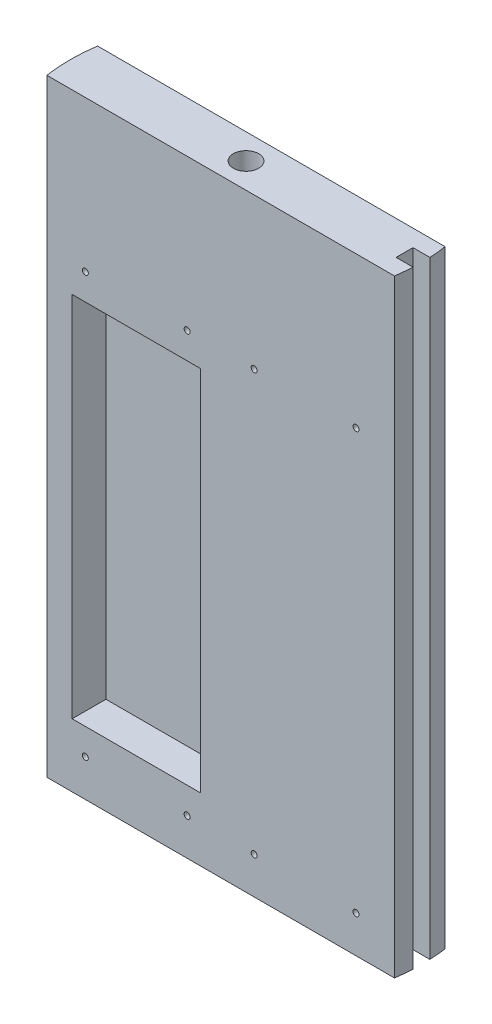
SolidWorks part; units mm, degrees
material "PE High Density"
ref_plane "Front" through (0, 0, 0) normal (0, 0, 1) x (1, 0, 0)
ref_plane "Top" through (0, 0, 0) normal (0, 1, 0) x (1, 0, 0)
ref_plane "Right" through (0, 0, 0) normal (1, 0, 0) x (0, 0, -1)
sketch "Sketch1" plane through (0, 0, 0) normal (0, 1, 0) x (1, 0, 0)
  line L0 (0, 9.525) -> (0, -9.525) construction
  line L1 (-65.3495, -9.525) -> (65.3495, -9.525)
  line L3 (-65.3495, 9.525) -> (65.3495, 9.525)
  arc A0 (-65.3495, 9.525) -> (-65.3495, -9.525) centre (0, 0) ccw
  circle A1 centre (0, 0) radius 66.04 construction
  arc A2 (65.3495, -9.525) -> (65.3495, 9.525) centre (0, 0) ccw
  point P0 (0, 0)
  point P3 (0, 0)
  dimension "D1" = 19.05
extrude "Boss-Extrude1" add sketch "Sketch1" against normal up to surface (228.6 mm away)
sketch "Sketch3" plane through (0, 0, 0) normal (0, 1, 0) x (1, 0, 0)
  line L0 (66.04, 0) -> (33.02, 0) construction
  line L1 (33.02, 0) -> (0, 0) construction
  line L2 (0, 0) -> (-33.02, 0) construction
  line L3 (-33.02, 0) -> (-66.04, 0) construction
  circle A0 centre (0, 0) radius 4.7625
  arc A3 (65.3495, -9.525) -> (65.3495, 9.525) centre (0, 0) ccw construction
  arc A4 (-65.3495, 9.525) -> (-65.3495, -9.525) centre (0, 0) ccw construction
  dimension "D1" = 9.525
extrude "Cut-Extrude1" cut sketch "Sketch3" against normal through all contours A0
hole_wizard "#4-40 Tapped Hole1" positions "Sketch4" profile "Sketch5" tap size "#4-40" standard "ANSI Inch" end condition through all
sketch "Sketch4" plane through (0, 0, 9.525) normal (0, 0, 1) x (1, 0, 0)
  point P0 (-50.8954, -56.7192)
  point P3 (-12.6046, -56.7192)
  point P15 (-12.6046, -214.6808)
  point P24 (-50.8954, -214.6808)
  point P32 (12.6046, -56.7192)
  point P35 (50.8954, -56.7192)
  point P40 (12.6046, -214.6808)
  point P43 (50.8954, -214.6808)
cosmetic thread "Hole Thread1" parameters "D2"=2.8448
cosmetic thread "Hole Thread8" parameters "D2"=2.8448
cosmetic thread "Hole Thread13" parameters "D2"=2.8448
cosmetic thread "Hole Thread14" parameters "D2"=2.8448
sketch "Sketch5" plane through (-50.8954, -56.7192, 9.525) normal (1, 0, 0) x (0, -1, 0)
  line L0 (0, 0) -> (0, 19.05)
  line L1 (0, 19.05) -> (1.1303, 19.05)
  line L2 (1.1303, 19.05) -> (1.1303, 0)
  line L5 (1.1303, 0) -> (0, 0)
  line L11 (0, -6.35) -> (0, 107.95) construction
  dimension "Thru Tap Drill Dia." = 2.2606
  dimension "Thru Tap Drill Depth" = 19.05
cosmetic thread "Hole Thread17" parameters "D2"=2.8448
cosmetic thread "Hole Thread18" parameters "D2"=2.8448
cosmetic thread "Hole Thread19" parameters "D2"=2.8448
cosmetic thread "Hole Thread20" parameters "D2"=2.8448
sketch "Sketch6" plane through (0, -228.6, 0) normal (0, -1, 0) x (1, 0, 0)
  line L0 (59.6136, -3.175) -> (65.9636, -3.175) construction
  line L1 (59.6136, 3.175) -> (65.9636, 3.175)
  line L2 (59.6136, 3.175) -> (59.6136, -3.175)
  line L3 (59.6136, -3.175) -> (65.9636, -3.175)
  arc A0 (65.3495, -9.525) -> (65.3495, 9.525) centre (0, 0) ccw construction
  arc A1 (65.9636, 3.175) -> (65.9636, -3.175) centre (0, 0) cw
extrude "Cut-Extrude2" cut sketch "Sketch6" against normal through all
sketch "Sketch7" plane through (0, 0, 9.525) normal (0, 0, 1) x (1, 0, 0)
  line L2 (-7.6625, -204.7875) -> (-55.8375, -204.7875)
  line L3 (-7.6625, -204.7875) -> (-7.6625, -66.6125)
  line L4 (-7.6625, -66.6125) -> (-55.8375, -66.6125)
  line L5 (-55.8375, -204.7875) -> (-55.8375, -66.6125)
extrude "Cut-Extrude3" cut sketch "Sketch7" against normal blind 12.7
sketch "Sketch8" plane through (0, 0, -9.525) normal (0, 0, -1) x (-1, 0, 0)
  line L0 (0, 0) -> (0, -228.6) construction
  line L1 (65.3495, -228.6) -> (-65.3495, -228.6) construction
  line L2 (7.6625, -66.6125) -> (55.8375, -66.6125) construction
  line L3 (-55.8375, -66.6125) -> (-7.6625, -66.6125)
  line L4 (-55.8375, -66.6125) -> (-55.8375, -204.7875)
  line L5 (-55.8375, -204.7875) -> (-7.6625, -204.7875)
  line L6 (-7.6625, -66.6125) -> (-7.6625, -204.7875)
  line L7 (7.6625, -204.7875) -> (7.6625, -66.6125) construction
  line L8 (-7.6625, -66.6125) -> (0, -66.6125) construction
  line L9 (0, -66.6125) -> (7.6625, -66.6125) construction
extrude "Cut-Extrude4" cut sketch "Sketch8" against normal blind 12.7
